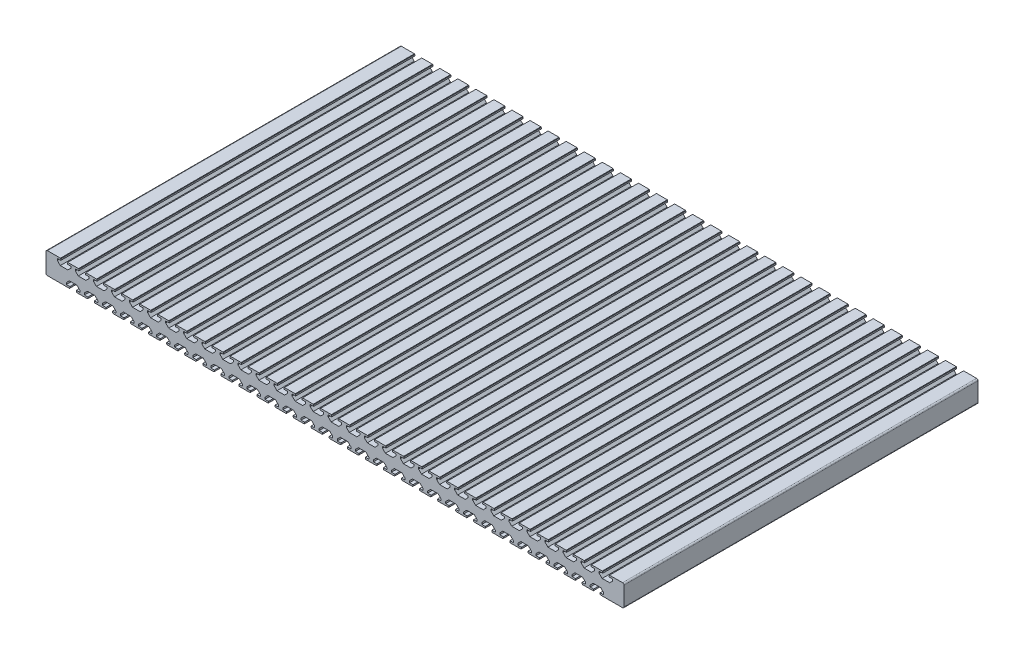
SolidWorks part; units mm, degrees
ref_plane "Front Plane" through (0, 0, 0) normal (0, 0, 1) x (1, 0, 0)
ref_plane "Top Plane" through (0, 0, 0) normal (0, 1, 0) x (1, 0, 0)
ref_plane "Right Plane" through (0, 0, 0) normal (1, 0, 0) x (0, 0, -1)
sketch "Sketch1" plane through (0, 0, 0) normal (0, 1, 0) x (1, 0, 0)
  line L1 (0, 0) -> (800, 0)
  line L2 (0, 0) -> (0, 490)
  line L3 (0, 490) -> (800, 490)
  line L4 (800, 0) -> (800, 490)
  dimension "D1" = 490
  dimension "D2" = 800
extrude "Boss-Extrude1" add sketch "Sketch1" along normal blind 30
sketch "Sketch2" plane through (0, 0, 0) normal (0, 0, 1) x (1, 0, 0)
  line L0 (20.5, 30) -> (20.5, 27.55)
  line L1 (0, 30) -> (800, 30) construction
  line L2 (20.5, 27.55) -> (15.65, 27.55)
  line L3 (15.65, 27.55) -> (15.65, 25.1)
  line L4 (15.65, 25.1) -> (19.75, 21)
  line L5 (19.75, 21) -> (30.25, 21)
  line L6 (30.25, 21) -> (34.35, 25.1)
  line L7 (34.35, 25.1) -> (34.35, 27.55)
  line L8 (34.35, 27.55) -> (29.5, 27.55)
  line L9 (29.5, 27.55) -> (29.5, 30)
  line L10 (29.5, 30) -> (20.5, 30)
  line L12 (20, 30) -> (20.5, 30)
  line L13 (20.5, 29.5) -> (20.5, 30)
  line L14 (29.5, 30) -> (29.5, 29.5)
  line L15 (30, 30) -> (29.5, 30)
  arc A0 (20.5, 29.5) -> (20, 30) centre (20.5, 30) cw
  arc A1 (30, 30) -> (29.5, 29.5) centre (29.5, 30) cw
  point P4 (25, 30)
  point P13 (25, 21)
  line M13 (800, 30) -> (0, 30)
  dimension "D6" = 0.5
  dimension "D7" = 0.5
  dimension "D1" = 9
  dimension "D2" = 9
  dimension "D3" = 2.45
  dimension "D4" = 10.5
  dimension "D5" = 20.5
extrude "Cut-Extrude1" cut sketch "Sketch2" against normal through all contours A0 L0 M13 | L8 L9 L0 L2 L3 L4 L5 L6 L7 M13
pattern_linear "LPattern1" count 31 spacing 25 along (1, 0, 0) of "Cut-Extrude1"
sketch "Sketch3" plane through (0, 0, 0) normal (0, 0, 1) x (1, 0, 0)
  line L0 (33, 0) -> (33, 2.45)
  line L1 (0, 0) -> (800, 0) construction
  line L2 (33, 2.45) -> (28.15, 2.45)
  line L3 (28.15, 2.45) -> (28.15, 4.9)
  line L4 (28.15, 4.9) -> (32.25, 9)
  line L5 (32.25, 9) -> (42.75, 9)
  line L6 (42.75, 9) -> (46.85, 4.9)
  line L7 (46.85, 4.9) -> (46.85, 2.45)
  line L8 (46.85, 2.45) -> (42, 2.45)
  line L9 (42, 2.45) -> (42, 0)
  line L10 (42, 0) -> (33, 0)
  line L11 (34.35, 27.55) -> (29.5, 27.55) construction
  line L12 (33, 0.5) -> (33, 0)
  line L13 (32.5, 0) -> (33, 0)
  line L14 (42, 0) -> (42.5, 0)
  line L15 (42, 0.5) -> (42, 0)
  arc A0 (33, 0.5) -> (32.5, 0) centre (33, 0) ccw
  arc A1 (42, 0.5) -> (42.5, 0) centre (42, 0) cw
  point P4 (37.5, 9)
  point P13 (37.5, 0)
  dimension "D6" = 0.5
  dimension "D1" = 10.5
  dimension "D2" = 9
  dimension "D3" = 2.45
  dimension "D4" = 9
  dimension "D5" = 32.5
extrude "Cut-Extrude2" cut sketch "Sketch3" against normal through all contours L10 L9 L8 L7 L6 L5 L4 L3 L2 L0 | L12 A0 L13 | L14 A1 L15
pattern_linear "LPattern2" count 30 spacing 25 along (1, 0, 0) of "Cut-Extrude2"
fillet "Fillet1" radius 2 4 edges at (800, 0, -245) (800, 30, -245) (0, 0, -245) (0, 30, -245)
